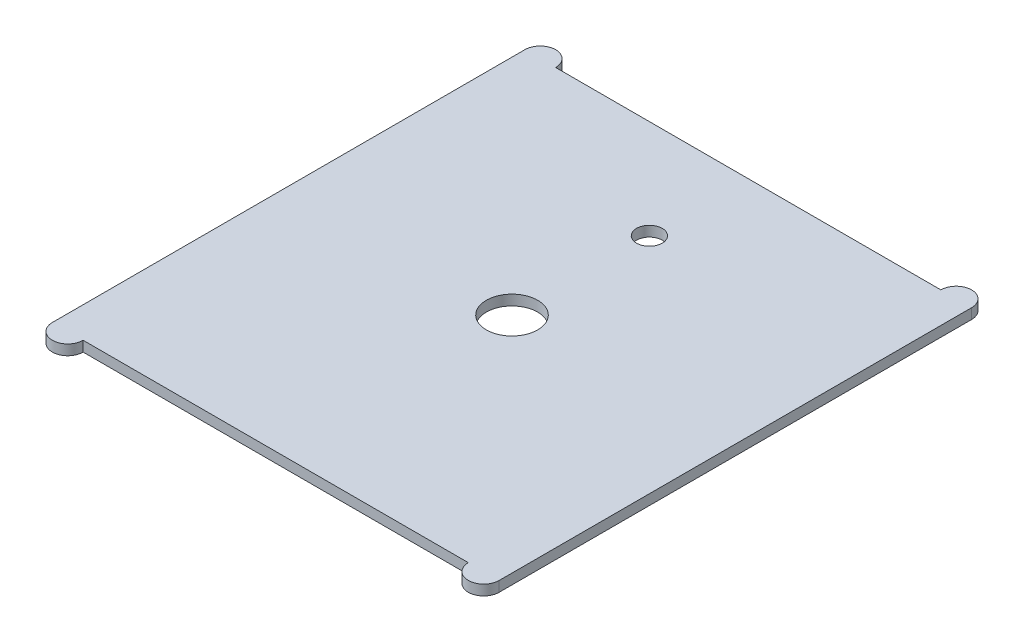
SolidWorks part; units mm, degrees
ref_plane "Front Plane" through (0, 0, 0) normal (0, 0, 1) x (1, 0, 0)
ref_plane "Top Plane" through (0, 0, 0) normal (0, 1, 0) x (1, 0, 0)
ref_plane "Right Plane" through (0, 0, 0) normal (1, 0, 0) x (0, 0, -1)
sketch "Sketch1" plane through (0, 0, 0) normal (0, 1, 0) x (1, 0, 0)
  line L1 (-187.5, 230) -> (187.5, 230)
  line L2 (-217.5, 230) -> (-217.5, -230)
  line L3 (-187.5, -230) -> (187.5, -230)
  line L4 (217.5, 230) -> (217.5, -230)
  line L5 (-217.5, 230) -> (217.5, -230) construction
  line L6 (-217.5, -230) -> (217.5, 230) construction
  arc A0 (-217.5, -230) -> (-187.5, -230) centre (-202.5, -230) ccw
  arc A1 (-217.5, 230) -> (-187.5, 230) centre (-202.5, 230) cw
  arc A2 (217.5, 230) -> (187.5, 230) centre (202.5, 230) ccw
  arc A3 (217.5, -230) -> (187.5, -230) centre (202.5, -230) cw
  circle A4 centre (0, 0) radius 25
  point P0 (0, 0)
  dimension "D7" = 50
  dimension "D1" = 460
  dimension "D2" = 435
  dimension "D3" = 30
  dimension "D4" = 30
  dimension "D5" = 30
  dimension "D6" = 30
extrude "Boss-Extrude2" add sketch "Sketch1" against normal blind 10
sketch "Sketch3" plane through (0, 0, 0) normal (0, 1, 0) x (1, 0, 0)
  line L1 (-217.5, 230) -> (-217.5, -230) construction
  circle A0 centre (0, 133.75) radius 12.5
  dimension "D1" = 25
  dimension "D2" = 133.75
  dimension "D3" = 217.5
extrude "Cut-Extrude3" cut sketch "Sketch3" against normal through all
